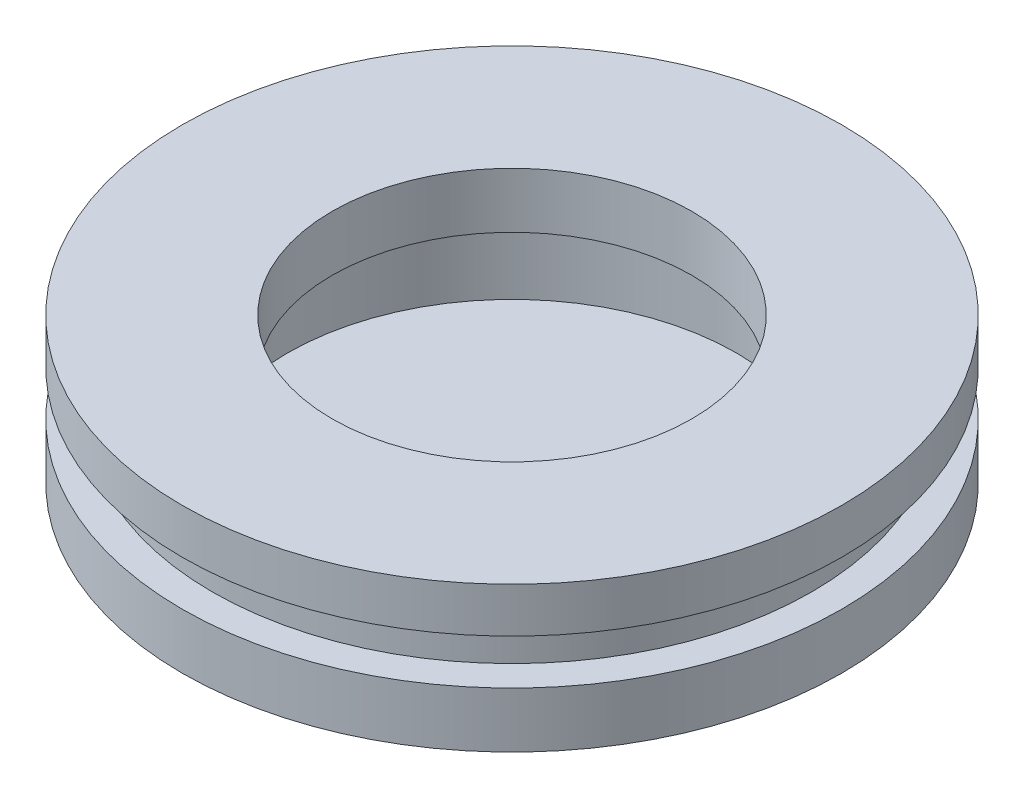
SolidWorks part; units mm, degrees
ref_plane "Front Plane" through (0, 0, 0) normal (0, 0, 1) x (1, 0, 0)
ref_plane "Top Plane" through (0, 0, 0) normal (0, 1, 0) x (1, 0, 0)
ref_plane "Right Plane" through (0, 0, 0) normal (1, 0, 0) x (0, 0, -1)
sketch "Sketch1" plane through (0, 0, 0) normal (0, 0, 1) x (1, 0, 0)
  line L0 (0, 0) -> (0, 8.8537)
  line L1 (0, 8.8537) -> (-11, 8.8537)
  line L2 (-11, 8.8537) -> (-11, 7.3537)
  line L3 (-11, 7.3537) -> (-10, 7.3537)
  line L4 (-10, 7.3537) -> (-10, 5.8537)
  line L5 (-10, 5.8537) -> (-11, 5.8537)
  line L6 (-11, 5.8537) -> (-11, 4.0037)
  line L7 (-11, 4.0037) -> (0, 0)
  dimension "D1" = 11
  dimension "D2" = 1.5
  dimension "D3" = 1.5
  dimension "D4" = 1.85
  dimension "D5" = 20
  dimension "D6" = 10
revolve "Revolve1" add sketch "Sketch1" angle 360 about L0
sketch "Sketch2" plane through (0, 0, 0) normal (0, 0, 1) x (1, 0, 0)
  line L0 (0, 4.0037) -> (0, 10.0037)
  line L1 (11, 4.0037) -> (-11, 4.0037) construction
  line L2 (0, 10.0037) -> (-6, 10.0037)
  line L3 (-6, 10.0037) -> (-6, 7.0037)
  line L4 (-6, 7.0037) -> (-7.5, 7.0037)
  line L5 (-7.5, 7.0037) -> (-7.5, 4.0037)
  line L6 (-7.5, 4.0037) -> (0, 4.0037)
  dimension "D1" = 6
  dimension "D2" = 7.5
  dimension "D3" = 3
  dimension "D4" = 3
revolve "Cut-Revolve1" cut sketch "Sketch2" angle 360 about L0
